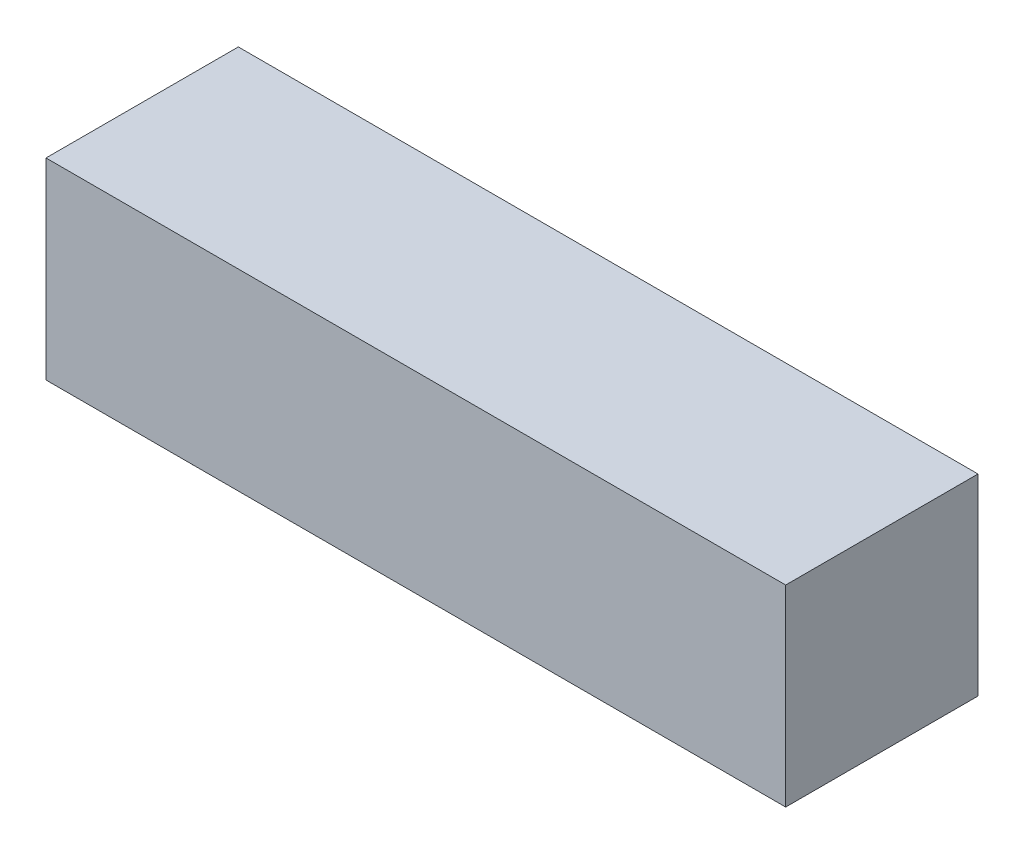
SolidWorks part; units mm, degrees
ref_plane "Plan de face" through (0, 0, 0) normal (0, 0, 1) x (1, 0, 0)
ref_plane "Plan de dessus" through (0, 0, 0) normal (0, 1, 0) x (1, 0, 0)
ref_plane "Plan de droite" through (0, 0, 0) normal (1, 0, 0) x (0, 0, -1)
sketch "Esquisse1" plane through (0, 0, 0) normal (0, 0, 1) x (1, 0, 0)
  line L1 (-22.6998, 11.311) -> (27.3002, 11.311)
  line L2 (-22.6998, 11.311) -> (-22.6998, -1.689)
  line L3 (-22.6998, -1.689) -> (27.3002, -1.689)
  line L4 (27.3002, 11.311) -> (27.3002, -1.689)
  dimension "D1" = 13
  dimension "D2" = 50
extrude "Boss.-Extru.1" add sketch "Esquisse1" along normal blind 13
